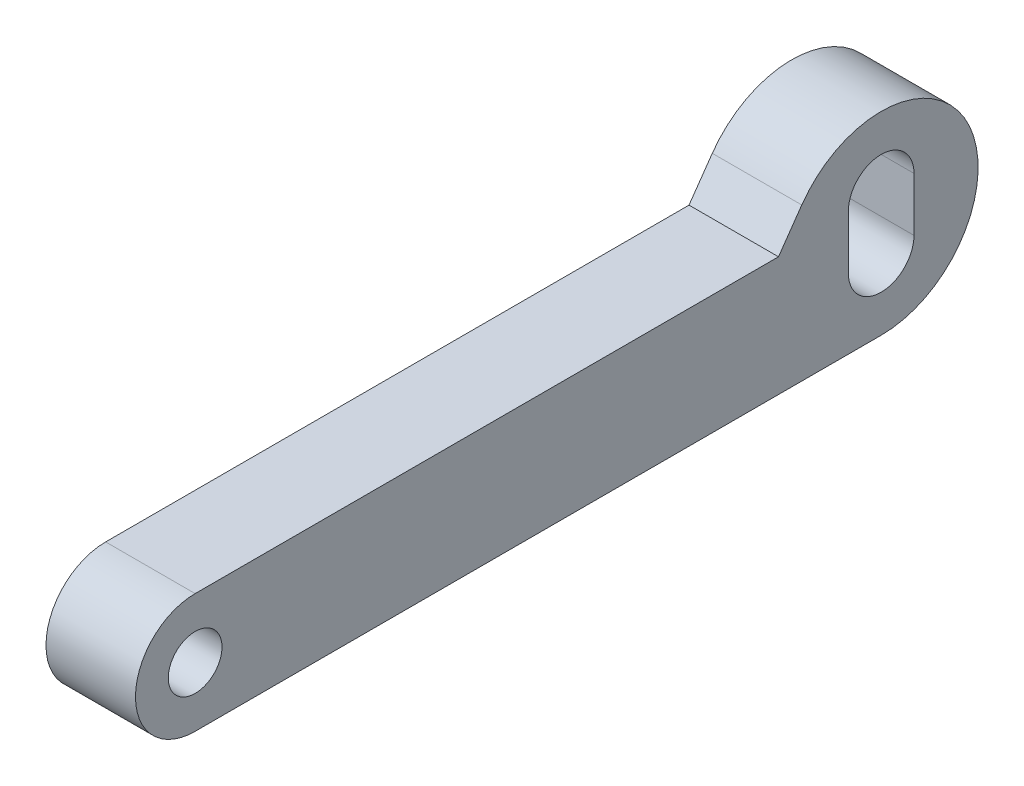
SolidWorks part; units mm, degrees
ref_plane "前视基准面" through (0, 0, 0) normal (0, 0, 1) x (1, 0, 0)
ref_plane "上视基准面" through (0, 0, 0) normal (0, 1, 0) x (1, 0, 0)
ref_plane "右视基准面" through (0, 0, 0) normal (1, 0, 0) x (0, 0, -1)
sketch "Sketch1" plane through (0, 0, 0) normal (1, 0, 0) x (0, 0, -1)
  line L0 (0, 12.8208) -> (0, 0) construction
  line L1 (23, 4.15) -> (23, 2.35) construction
  line L2 (24.1, 4.15) -> (24.1, 2.35)
  line L3 (21.9, 4.15) -> (21.9, 2.35)
  line L4 (0, 0) -> (23, 0)
  line L5 (0, 4) -> (19.5576, 4)
  line L6 (19.5576, 4) -> (20.3378, 5.1141)
  arc A0 (24.1, 4.15) -> (21.9, 4.15) centre (23, 4.15) ccw
  arc A1 (21.9, 2.35) -> (24.1, 2.35) centre (23, 2.35) ccw
  arc A2 (23, 0) -> (20.3378, 5.1141) centre (23, 3.25) ccw
  arc A3 (0, 4) -> (0, 0) centre (0, 2) ccw
  circle A4 centre (0, 2) radius 0.9
  point P5 (23, 3.25)
  dimension "D3" = 6.5
  dimension "D5" = 1.8
  dimension "D1" = 1.8
  dimension "D2" = 2.2
  dimension "D4" = 125
  dimension "D6" = 4
  dimension "D7" = 23
extrude "Extrude1" add sketch "Sketch1" along normal blind 3
